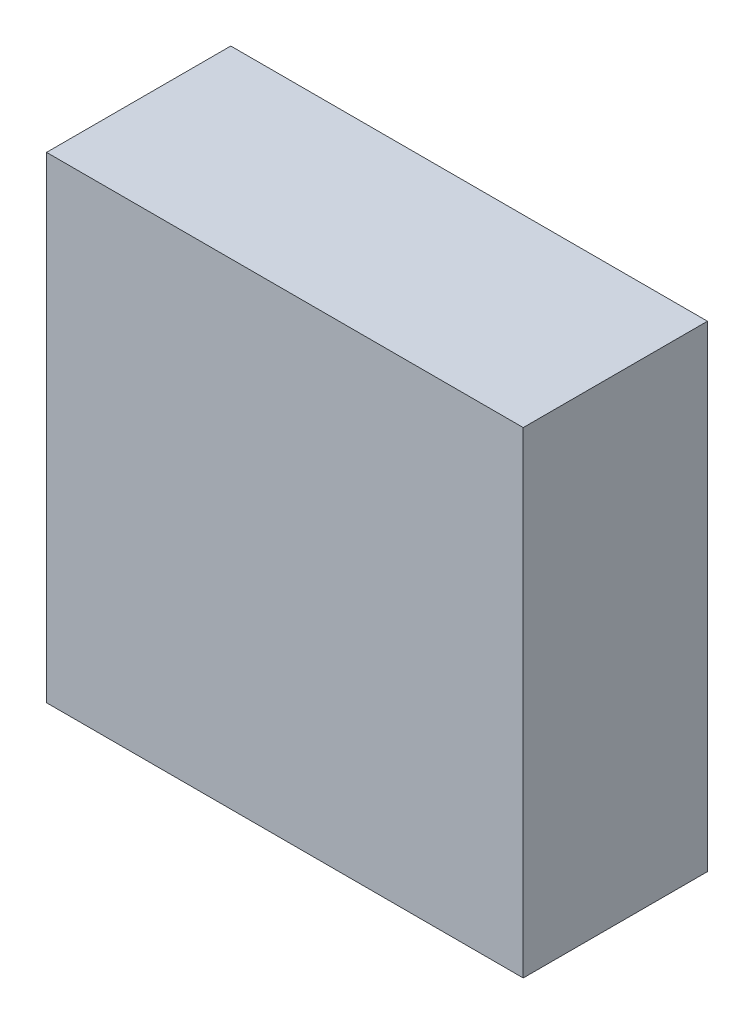
SolidWorks part; units mm, degrees
ref_plane "Front Plane" through (0, 0, 0) normal (0, 0, 1) x (1, 0, 0)
ref_plane "Top Plane" through (0, 0, 0) normal (0, 1, 0) x (1, 0, 0)
ref_plane "Right Plane" through (0, 0, 0) normal (1, 0, 0) x (0, 0, -1)
sketch "Sketch1" plane through (0, 0, 0) normal (0, 0, 1) x (1, 0, 0)
  line L1 (0, 0) -> (59, 0)
  line L2 (0, 0) -> (0, 59)
  line L3 (0, 59) -> (59, 59)
  line L4 (59, 0) -> (59, 59)
extrude "Boss-Extrude1" add sketch "Sketch1" along normal blind 22.8
